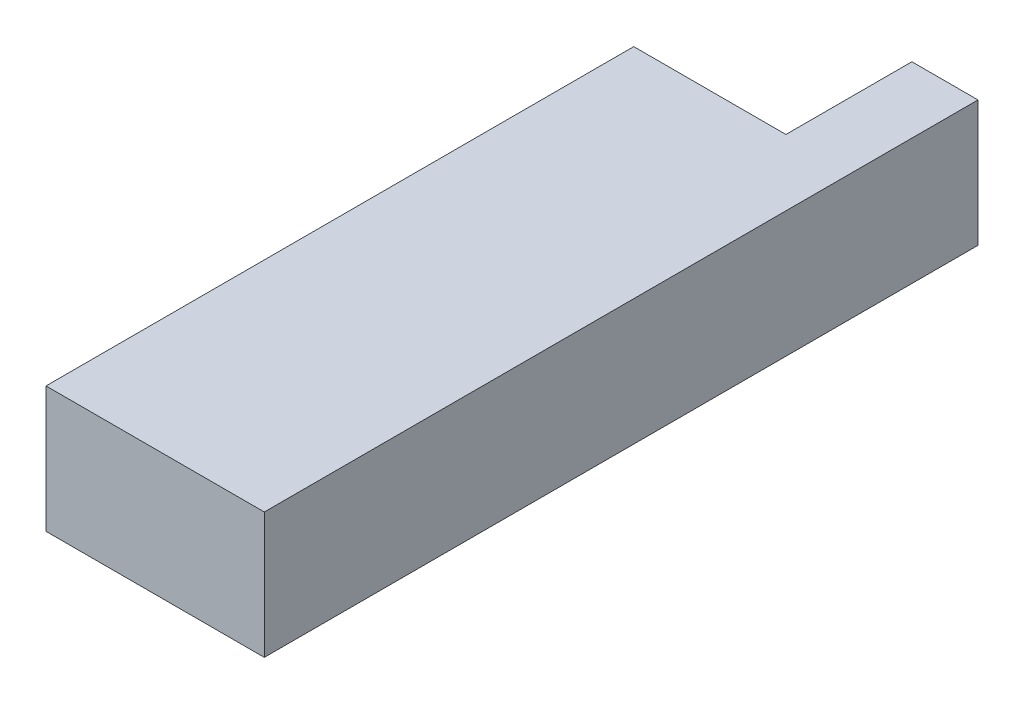
SolidWorks part; units mm, degrees
ref_plane "Front Plane" through (0, 0, 0) normal (0, 0, 1) x (1, 0, 0)
ref_plane "Top Plane" through (0, 0, 0) normal (0, 1, 0) x (1, 0, 0)
ref_plane "Right Plane" through (0, 0, 0) normal (1, 0, 0) x (0, 0, -1)
sketch "Sketch1" plane through (0, 0, 0) normal (0, 1, 0) x (1, 0, 0)
  line L1 (-16.51, 44.45) -> (16.51, 44.45)
  line L2 (-16.51, 44.45) -> (-16.51, -44.45)
  line L3 (-16.51, -44.45) -> (16.51, -44.45)
  line L4 (16.51, 44.45) -> (16.51, -44.45)
  line L5 (-16.51, 44.45) -> (16.51, -44.45) construction
  line L6 (-16.51, -44.45) -> (16.51, 44.45) construction
  point P0 (0, 0)
  dimension "D1" = 33.02
  dimension "D2" = 88.9
extrude "Boss-Extrude1" add sketch "Sketch1" along normal mid plane 19.05
sketch "Sketch2" plane through (0, 0, -44.45) normal (0, 0, -1) x (-1, 0, 0)
  line L0 (-16.51, -9.525) -> (16.51, -9.525) construction
  line L1 (-16.51, 9.525) -> (-6.51, 9.525)
  line L2 (-16.51, 9.525) -> (-16.51, -9.525)
  line L3 (-16.51, -9.525) -> (-6.51, -9.525)
  line L4 (-6.51, 9.525) -> (-6.51, -9.525)
  dimension "D1" = 10
extrude "Boss-Extrude2" add sketch "Sketch2" along normal blind 19.05
